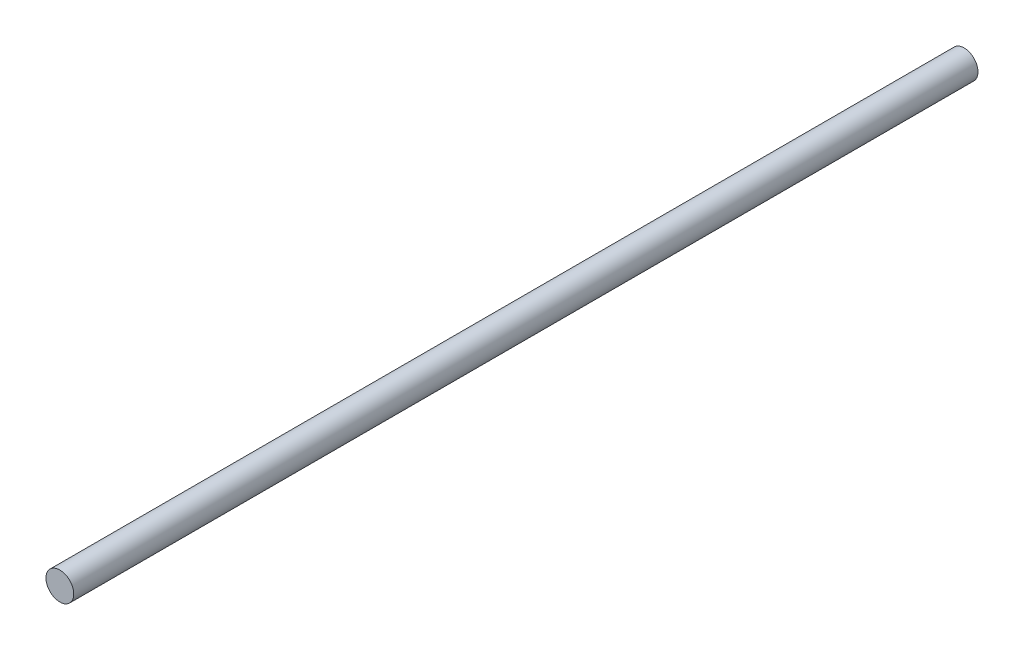
SolidWorks part; units mm, degrees
ref_plane "Płaszczyzna przednia" through (0, 0, 0) normal (0, 0, 1) x (1, 0, 0)
ref_plane "Płaszczyzna górna" through (0, 0, 0) normal (0, 1, 0) x (1, 0, 0)
ref_plane "Płaszczyzna prawa" through (0, 0, 0) normal (1, 0, 0) x (0, 0, -1)
sketch "Sketch1" plane through (0, 0, 0) normal (0, 0, 1) x (1, 0, 0)
  circle A0 centre (0, 0) radius 8
  dimension "D1" = 16
extrude "Boss-Extrude1" add sketch "Sketch1" along normal blind 521
